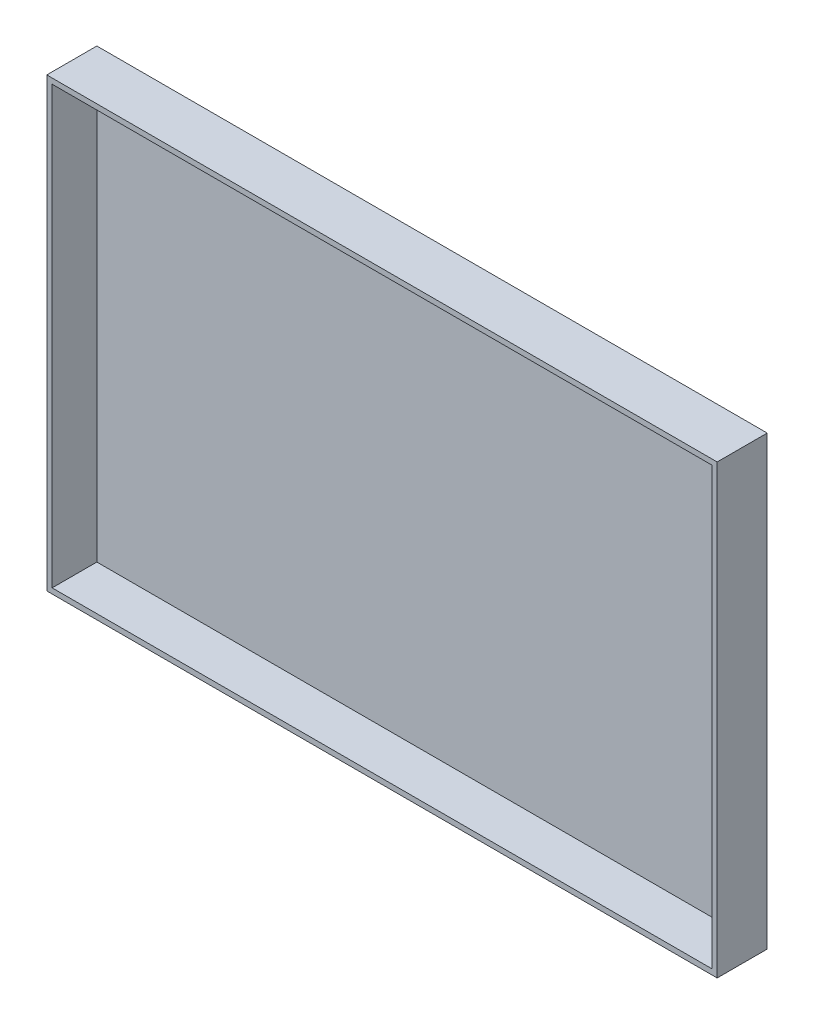
SolidWorks part; units mm, degrees
ref_plane "Alzado" through (0, 0, 0) normal (0, 0, 1) x (1, 0, 0)
ref_plane "Planta" through (0, 0, 0) normal (0, 1, 0) x (1, 0, 0)
ref_plane "Vista lateral" through (0, 0, 0) normal (1, 0, 0) x (0, 0, -1)
sketch "Croquis1" plane through (0, 0, 0) normal (0, 0, 1) x (1, 0, 0)
  line L1 (-186.3964, 66.4286) -> (-36.3964, 66.4286)
  line L2 (-186.3964, 66.4286) -> (-186.3964, -33.5714)
  line L3 (-186.3964, -33.5714) -> (-36.3964, -33.5714)
  line L4 (-36.3964, 66.4286) -> (-36.3964, -33.5714)
  dimension "D1" = 150
  dimension "D2" = 100
extrude "Saliente-Extruir1" add sketch "Croquis1" along normal blind 1.2
sketch "Croquis2" plane through (0, 0, 1.2) normal (0, 0, 1) x (1, 0, 0)
  line L1 (-186.3964, 66.4286) -> (-36.3964, 66.4286)
  line L2 (-186.3964, 66.4286) -> (-186.3964, -33.5714)
  line L3 (-186.3964, -33.5714) -> (-36.3964, -33.5714)
  line L4 (-36.3964, 66.4286) -> (-36.3964, -33.5714)
  line L5 (-185.1964, 65.2286) -> (-37.5964, 65.2286)
  line L6 (-185.1964, 65.2286) -> (-185.1964, -32.3714)
  line L7 (-185.1964, -32.3714) -> (-37.5964, -32.3714)
  line L8 (-37.5964, 65.2286) -> (-37.5964, -32.3714)
  dimension "D1" = 1.2
  dimension "D2" = 1.2
  dimension "D3" = 1.2
  dimension "D4" = 1.2
extrude "Saliente-Extruir2" add sketch "Croquis2" along normal blind 10
